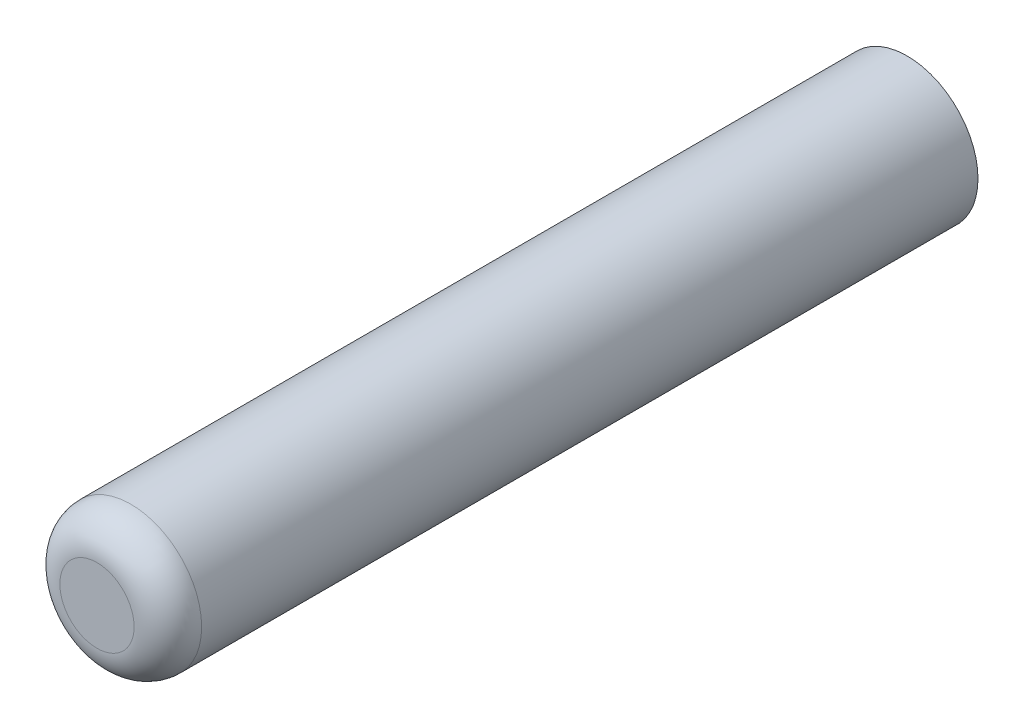
SolidWorks part; units mm, degrees
ref_plane "Front Plane" through (0, 0, 0) normal (0, 0, 1) x (1, 0, 0)
ref_plane "Top Plane" through (0, 0, 0) normal (0, 1, 0) x (1, 0, 0)
ref_plane "Right Plane" through (0, 0, 0) normal (1, 0, 0) x (0, 0, -1)
sketch "Sketch1" plane through (0, 0, 0) normal (0, 0, 1) x (1, 0, 0)
  circle A0 centre (0, 0) radius 1.05
  dimension "D1" = 2.1
extrude "Boss-Extrude1" add sketch "Sketch1" along normal blind 12
fillet "Fillet1" radius 0.5 1 edges at (1.05, 0, 12)
